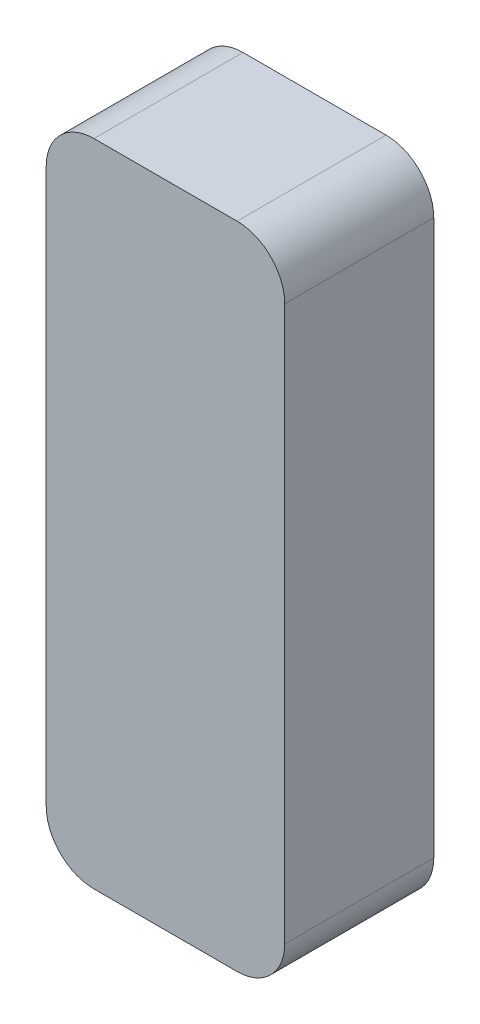
SolidWorks part; units mm, degrees
material "PET"
ref_plane "Front Plane" through (0, 0, 0) normal (0, 0, 1) x (1, 0, 0)
ref_plane "Top Plane" through (0, 0, 0) normal (0, 1, 0) x (1, 0, 0)
ref_plane "Right Plane" through (0, 0, 0) normal (1, 0, 0) x (0, 0, -1)
sketch "Sketch1" plane through (0, 0, 0) normal (0, 0, 1) x (1, 0, 0)
  line L1 (-20, 54.5) -> (20, 54.5)
  line L2 (-20, 54.5) -> (-20, -54.5)
  line L3 (-20, -54.5) -> (20, -54.5)
  line L4 (20, 54.5) -> (20, -54.5)
  line L5 (-20, 54.5) -> (20, -54.5) construction
  line L6 (-20, -54.5) -> (20, 54.5) construction
  point P0 (0, 0)
  dimension "D1" = 109
  dimension "D2" = 40
extrude "Boss-Extrude1" add sketch "Sketch1" along normal blind 25
fillet "Fillet1" radius 8 4 edges at (-20, -54.5, 12.5) (20, -54.5, 12.5) (-20, 54.5, 12.5) (20, 54.5, 12.5)
